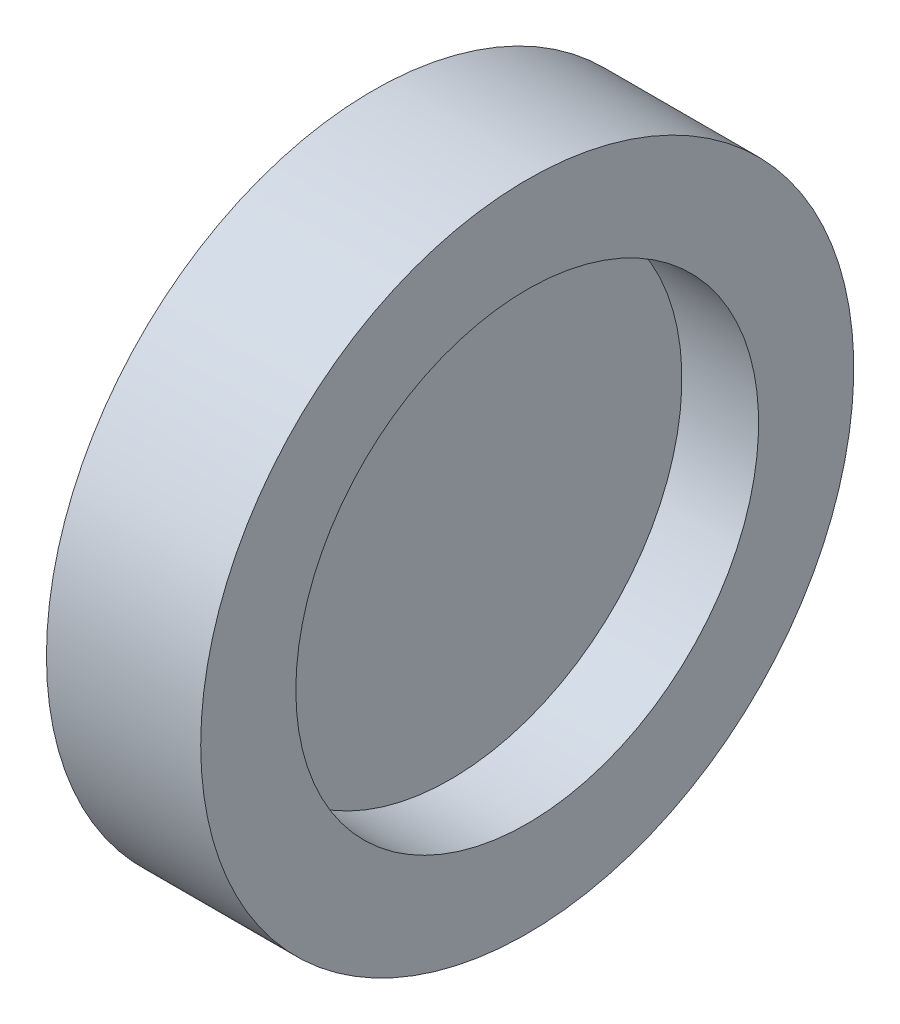
SolidWorks part; units mm, degrees
ref_plane "前视基准面" through (0, 0, 0) normal (0, 0, 1) x (1, 0, 0)
ref_plane "上视基准面" through (0, 0, 0) normal (0, 1, 0) x (1, 0, 0)
ref_plane "右视基准面" through (0, 0, 0) normal (1, 0, 0) x (0, 0, -1)
sketch "草图1" plane through (0, 0, 0) normal (0, 0, 1) x (1, 0, 0)
  line L0 (-0.0145, 9) -> (-0.0145, 0)
  line L2 (-0.0145, 9) -> (0.0145, 9)
  line L3 (-0.0145, 0) -> (0.0145, 0)
  line L4 (0.0145, 9) -> (0.0145, 0)
revolve "旋转2" add sketch "草图1" angle 360 about L3
sketch "草图4" plane through (0, 0, 0) normal (0, 0, 1) x (1, 0, 0)
  line L0 (-3, 12.7) -> (3, 12.7)
  line L1 (3, 12.7) -> (3, 9)
  line L2 (3, 9) -> (-3, 9)
  line L3 (0.0145, 9) -> (-0.0145, 9) construction
  line L4 (-3, 9) -> (-3, 12.7)
  line L5 (0, 9) -> (0, 12.7) construction
  line L6 (-1.6142, 0) -> (1.5903, 0) construction
revolve "旋转3" add sketch "草图4" angle 360 about L6
equation "\"D1@草图4\"=\"D1@草图1\""
